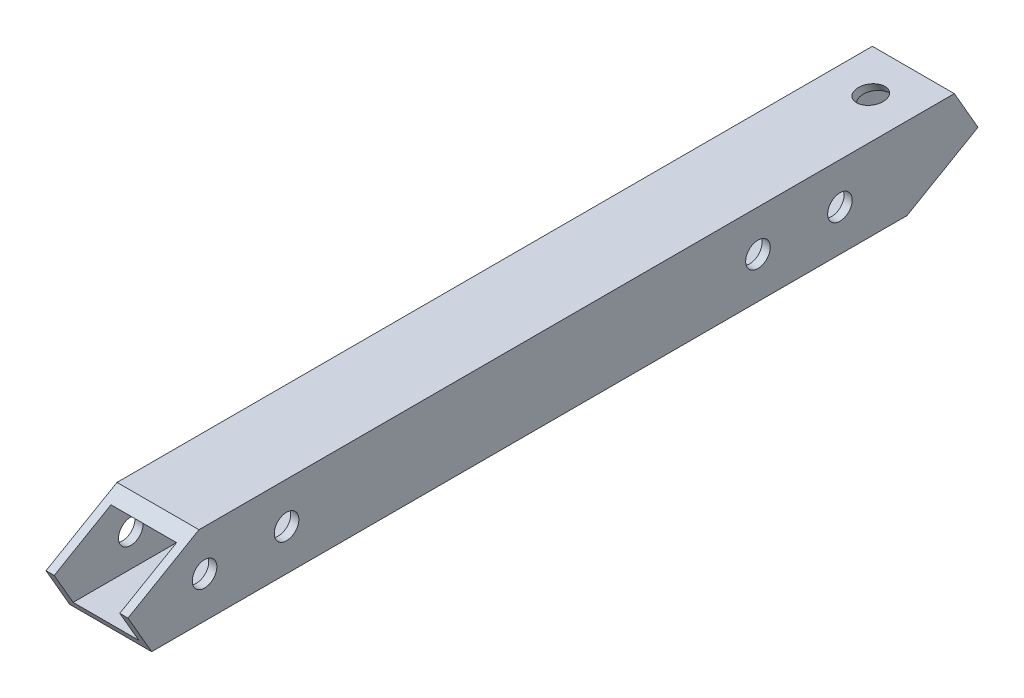
SolidWorks part; units mm, degrees
material "6063-O"
ref_plane "前视基准面" through (0, 0, 0) normal (0, 0, 1) x (1, 0, 0)
ref_plane "上视基准面" through (0, 0, 0) normal (0, 1, 0) x (1, 0, 0)
ref_plane "右视基准面" through (0, 0, 0) normal (1, 0, 0) x (0, 0, -1)
other "Configuration Table"
sketch "草图1" plane through (0, 0, 0) normal (0, 0, 1) x (1, 0, 0)
  line L1 (-5, 5) -> (5, 5)
  line L2 (-5, 5) -> (-5, -5)
  line L3 (-5, -5) -> (5, -5)
  line L4 (5, 5) -> (5, -5)
  line L5 (-5, 5) -> (5, -5) construction
  line L6 (-5, -5) -> (5, 5) construction
  point P4 (0, 0)
  dimension "D1" = 10
  dimension "D2" = 10
extrude "拉伸-薄壁1" add sketch "草图1" along normal blind 121 thin
sketch "草图2" plane through (5, 0, 0) normal (1, 0, 0) x (0, 0, -1)
  line L0 (0, 0) -> (-13, 0) construction
  line L1 (0, -5) -> (0, 5) construction
  line L2 (-121, 5) -> (-121, -5) construction
  line L4 (-112.3397, 0) -> (-103.6795, 5)
  line L5 (-121, 5) -> (0, 5) construction
  line L6 (-103.6795, 5) -> (-121, 5)
  line L7 (-121, 5) -> (-121, -5)
  line L8 (-121, 0) -> (-13, 0) construction
  line L9 (-8.6603, 0) -> (-17.3205, -5)
  line L10 (-121, -5) -> (0, -5) construction
  line L11 (-17.3205, -5) -> (0, -5)
  line L12 (0, -5) -> (0, 5)
  line L13 (-8.6603, 0) -> (-11.547, 5)
  line L14 (-11.547, 5) -> (0, 5)
  line L15 (-121, 5) -> (0, 5) construction
  line L16 (-112.3397, 0) -> (-109.453, -5)
  line L17 (-121, -5) -> (0, -5) construction
  line L18 (-109.453, -5) -> (-121, -5)
  line L19 (-112.3397, 0) -> (-121, -5) construction
  line L20 (-8.6603, 0) -> (0, 5) construction
  line L21 (-12.5574, -2.25) -> (-15.2074, 2.3399) construction
  circle A2 centre (-103, 0) radius 1.5
  circle A3 centre (-35.5, 0) radius 1.5
  circle A4 centre (-25.5, 0) radius 1.5
  circle A5 centre (-15.2074, 2.3399) radius 1.5 construction
  circle A6 centre (-93, 0) radius 1.5
  dimension "D5" = 18
  dimension "D3" = 60
  dimension "D6" = 10
  dimension "D7" = 85.5
  dimension "D10" = 10
  dimension "D2" = 3
  dimension "D11" = 4.5
  dimension "D4" = 5.3
  dimension "D8" = 60
  dimension "D9" = 121
extrude "切除-拉伸1" cut sketch "草图2" against normal through all
ref_plane "基准面1" through (0, 8.75, 5.0518) normal (0, 0.866, 0.5) x (1, 0, 0)
sketch "草图3" plane through (0, 8.75, 5.0518) normal (0, 0.866, 0.5) x (1, 0, 0)
  line L0 (0, -7.5) -> (0, -19.4742) construction
  line L1 (-5, -7.5) -> (5, -7.5) construction
  circle A0 centre (0, -12) radius 1.5
  dimension "D1" = 3
  dimension "D2" = 4.5
extrude "切除-拉伸2" cut sketch "草图3" against normal through all and the other way through all
